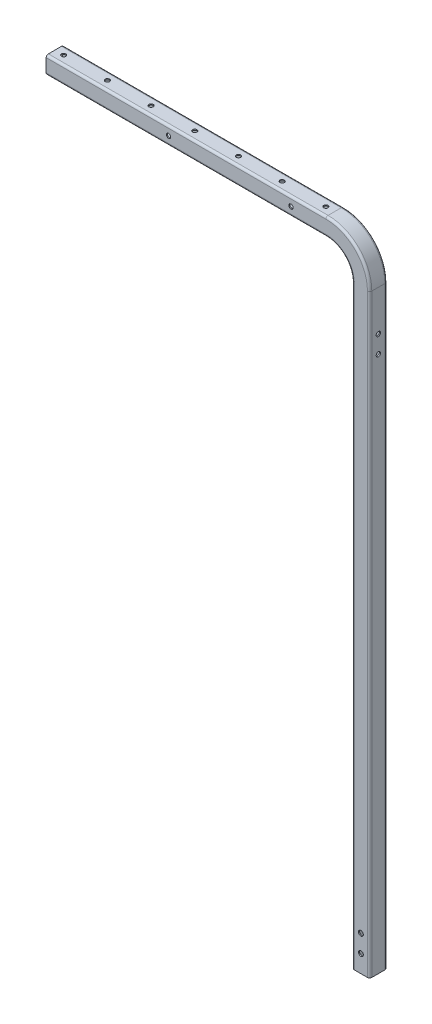
SolidWorks part; units mm, degrees
material "3003 Alloy"
ref_plane "Front" through (0, 0, 0) normal (0, 0, 1) x (1, 0, 0)
ref_plane "Top" through (0, 0, 0) normal (0, 1, 0) x (1, 0, 0)
ref_plane "Right" through (0, 0, 0) normal (1, 0, 0) x (0, 0, -1)
sketch "Sketch1" plane through (0, 0, 0) normal (0, 0, 1) x (1, 0, 0)
  line L0 (0, 0) -> (406.4, 0)
  line L1 (457.2, -50.8) -> (457.2, -914.4)
  arc A0 (457.2, -50.8) -> (406.4, 0) centre (406.4, -50.8) ccw
  dimension "D1" = 50.8
  dimension "D2" = 457.2
  dimension "D3" = 914.4
sketch "Sketch2"
  line L0 (-12.7, 12.7) -> (12.7, 12.7)
  line L1 (-12.7, 12.7) -> (-12.7, -12.7)
  line L2 (12.7, -12.7) -> (-12.7, -12.7)
  line L3 (12.7, -12.7) -> (12.7, 12.7)
  line L4 (12.7, 12.7) -> (-12.7, -12.7) construction
  dimension "square" = 25.4
sweep "Base-Sweep" add profiles "Sketch2" path "Sketch1"
fillet "Fillet1" radius 3.175 12 edges at (451.3013, -5.8987, 12.7) (451.3013, -5.8987, -12.7) (433.3408, -23.8592, -12.7) (433.3408, -23.8592, 12.7) (469.9, -482.6, 12.7) (469.9, -482.6, -12.7) (444.5, -482.6, -12.7) (444.5, -482.6, 12.7) (203.2, 12.7, 12.7) (203.2, 12.7, -12.7) (203.2, -12.7, -12.7) (203.2, -12.7, 12.7)
shell "Shell1" thickness 1.5875
sketch "Sketch3" plane through (0, 12.7, 0) normal (0, 1, 0) x (-1, 0, 0)
  line L0 (0, 0) -> (-406.4, 0) construction
  line L1 (0, 9.525) -> (0, -9.525) construction
  circle A0 centre (-12.7, 0) radius 3.175
  dimension "D2" = 6.35
  dimension "D1" = 12.7
extrude "Wood Hole" cut sketch "Sketch3" against normal up to next (1.5875 mm away)
pattern_linear "LPattern1" count 7 spacing 63.5 along (1, 0, 0) of "Wood Hole"
sketch "Sketch5" plane through (469.9, 0, 0) normal (1, 0, 0) x (0, 0, -1)
  line L4 (-9.525, 12.7) -> (9.525, 12.7) construction
  line L5 (0, 50) -> (0, -50) construction
  circle A4 centre (0, -109.5375) radius 3.175
  circle A5 centre (0, -134.9375) radius 3.175
  dimension "D1" = 122.2375
  dimension "D3" = 6.35
  dimension "D2" = 25.4
extrude "cont_mtg" cut sketch "Sketch5" against normal through all
hole_wizard "1/4 (0.25) Diameter Hole1" positions "Sketch7" profile "Sketch6" hole size "1/4" standard "Ansi Inch" end condition through all
sketch "Sketch7" plane through (0, 0, 12.7) normal (0, 0, 1) x (1, 0, 0)
  line L1 (0, 9.525) -> (0, -9.525) construction
  line L2 (0, 0) -> (406.4, 0) construction
  point P0 (177.8, 0)
  point P1 (355.6, 0)
  dimension "D1" = 177.8
  dimension "D2" = 355.6
sketch "Sketch6" plane through (177.8, 0, 12.7) normal (1, 0, 0) x (0, -1, 0)
  line L0 (0, 0) -> (0, 25.4)
  line L1 (0, 25.4) -> (3.175, 25.4)
  line L2 (3.175, 25.4) -> (3.175, 0)
  line L5 (3.175, 0) -> (0, 0)
  line L11 (0, -6.35) -> (0, 107.95) construction
  dimension "Thru Hole Dia." = 6.35
  dimension "Thru Hole Depth" = 25.4
sketch "Sketch8" plane through (0, 0, -12.7) normal (0, 0, -1) x (-1, 0, 0)
  line L1 (-447.675, -914.4) -> (-466.725, -914.4) construction
  line L2 (-457.2, -50.8) -> (-457.2, -914.4) construction
  circle A1 centre (-457.2, -889) radius 3.5719
  dimension "D1" = 7.1437
  dimension "D3" = 25.4
extrude "Cut-Extrude1" cut sketch "Sketch8" against normal through all
pattern_linear "LPattern2" count 2 spacing 25.4 along (0, 1, 0) of "Cut-Extrude1"
